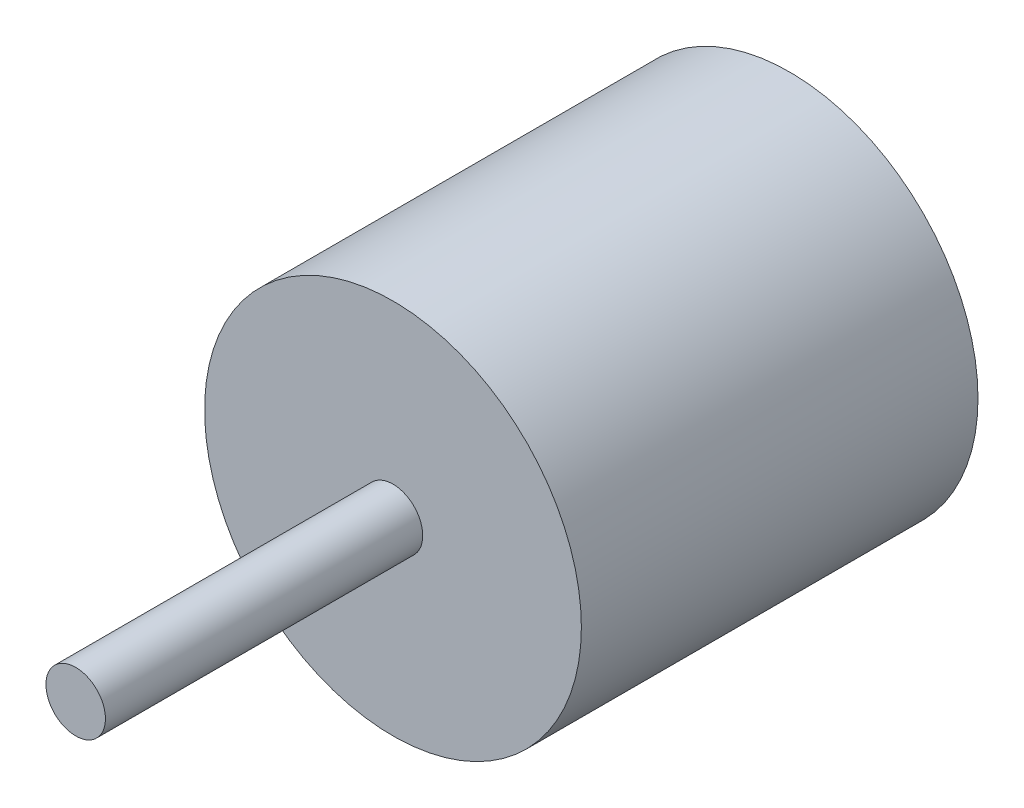
SolidWorks part; units mm, degrees
ref_plane "Front Plane" through (0, 0, 0) normal (0, 0, 1) x (1, 0, 0)
ref_plane "Top Plane" through (0, 0, 0) normal (0, 1, 0) x (1, 0, 0)
ref_plane "Right Plane" through (0, 0, 0) normal (1, 0, 0) x (0, 0, -1)
sketch "Sketch1" plane through (0, 0, 0) normal (0, 0, 1) x (1, 0, 0)
  circle A0 centre (26.3872, 15.3808) radius 19
  dimension "D1" = 38
extrude "Boss-Extrude1" add sketch "Sketch1" along normal blind 40
sketch "Sketch3" plane through (0, 0, 40) normal (0, 0, 1) x (1, 0, 0)
  circle A0 centre (26.3872, 15.3808) radius 3
  dimension "D1" = 6
extrude "Boss-Extrude2" add sketch "Sketch3" along normal blind 32
